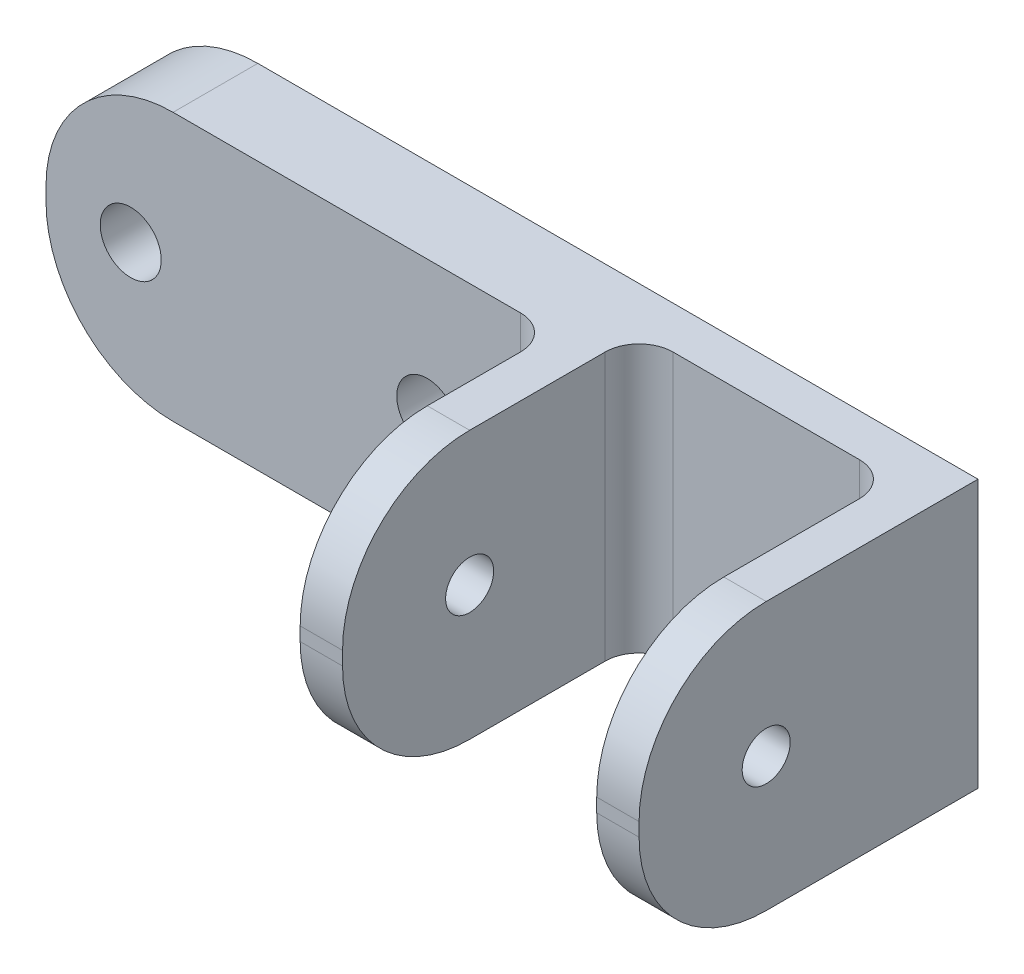
SolidWorks part; units mm, degrees
ref_plane "Front" through (0, 0, 0) normal (0, 0, 1) x (1, 0, 0)
ref_plane "Top" through (0, 0, 0) normal (0, 1, 0) x (1, 0, 0)
ref_plane "Right" through (0, 0, 0) normal (1, 0, 0) x (0, 0, -1)
sketch "Sketch1" plane through (0, 0, 0) normal (0, 0, 1) x (1, 0, 0)
  line L1 (-31.75, -10.033) -> (31.75, -10.033)
  line L2 (-31.75, -10.033) -> (-31.75, 10.033)
  line L3 (-31.75, 10.033) -> (31.75, 10.033)
  line L4 (31.75, -10.033) -> (31.75, 10.033)
  line L5 (-31.75, -10.033) -> (31.75, 10.033) construction
  line L6 (-31.75, 10.033) -> (31.75, -10.033) construction
  point P0 (0, 0)
  dimension "D1" = 20.066
  dimension "D2" = 63.5
extrude "Boss-Extrude1" add sketch "Sketch1" along normal blind 6.35
sketch "Sketch2" plane through (31.75, 0, 0) normal (1, 0, 0) x (0, 0, -1)
  line L1 (0, -10.033) -> (-25.4, -10.033)
  line L2 (0, -10.033) -> (0, 10.033)
  line L3 (0, 10.033) -> (-25.4, 10.033)
  line L4 (-25.4, -10.033) -> (-25.4, 10.033)
  point P5 (0, 10.033)
  dimension "D1" = 25.4
extrude "Boss-Extrude2" add sketch "Sketch2" against normal blind 3.175
sketch "Sketch4" plane through (0, 0, 6.35) normal (0, 0, 1) x (1, 0, 0)
  line L0 (28.575, 10.033) -> (-31.75, 10.033) construction
  line L1 (9.525, 10.033) -> (6.35, 10.033)
  line L2 (9.525, 10.033) -> (9.525, -10.033)
  line L3 (9.525, -10.033) -> (6.35, -10.033)
  line L4 (6.35, 10.033) -> (6.35, -10.033)
  line L5 (-31.75, -10.033) -> (28.575, -10.033) construction
  line L6 (28.575, 10.033) -> (31.75, 10.033) construction
  line L7 (28.575, 10.033) -> (28.575, -10.033) construction
  dimension "D1" = 19.05
extrude "Boss-Extrude3" add sketch "Sketch4" along normal up to surface (19.05 mm away) up to face at (30.1625, 0, 25.4)
sketch "Sketch3" plane through (28.575, 0, 0) normal (-1, 0, 0) x (0, 0, 1)
  line L0 (15.875, 10.033) -> (15.875, -10.033) construction
  line L1 (6.35, 10.033) -> (25.4, 10.033) construction
  line L2 (25.4, -10.033) -> (6.35, -10.033) construction
  circle A0 centre (15.875, 0) radius 1.8
  dimension "D1" = 3.6
extrude "Cut-Extrude1" cut sketch "Sketch3" against normal through all both and the other way through all
sketch "Sketch5" plane through (0, 0, 6.35) normal (0, 0, 1) x (1, 0, 0)
  line L0 (6.35, 0) -> (-31.75, 0) construction
  line L1 (6.35, 10.033) -> (6.35, -10.033) construction
  line L2 (-31.75, 10.033) -> (-31.75, -10.033) construction
  circle A0 centre (-3.175, 0) radius 2.286
  circle A1 centre (-25.4, 0) radius 2.286
  dimension "D3" = 4.572
  dimension "D1" = 9.525
  dimension "D2" = 6.35
extrude "Cut-Extrude2" cut sketch "Sketch5" against normal through all
sketch "Sketch6" plane through (0, 0, 6.35) normal (0, 0, 1) x (1, 0, 0)
  line L4 (9.525, 10.033) -> (9.525, -10.033)
  line L5 (9.525, -10.033) -> (28.575, -10.033)
  line L6 (28.575, -10.033) -> (28.575, 10.033)
  line L7 (28.575, 10.033) -> (9.525, 10.033)
  line L8 (9.525, 10.033) -> (9.525, -10.033)
  line L9 (9.525, -10.033) -> (28.575, -10.033)
  line L10 (28.575, -10.033) -> (28.575, 10.033)
  line L11 (28.575, 10.033) -> (9.525, 10.033)
  dimension "D1" = 0
extrude "Cut-Extrude3" cut sketch "Sketch6" against normal blind 3.175
fillet "Fillet1" radius 2.54 3 edges at (28.575, 0, 3.175) (9.525, 0, 3.175) (6.35, 0, 6.35)
fillet "Fillet2" radius 9.525 6 edges at (-31.75, -10.033, 3.175) (-31.75, 10.033, 3.175) (7.9375, -10.033, 25.4) (30.1625, -10.033, 25.4) (30.1625, 10.033, 25.4) (7.9375, 10.033, 25.4)
